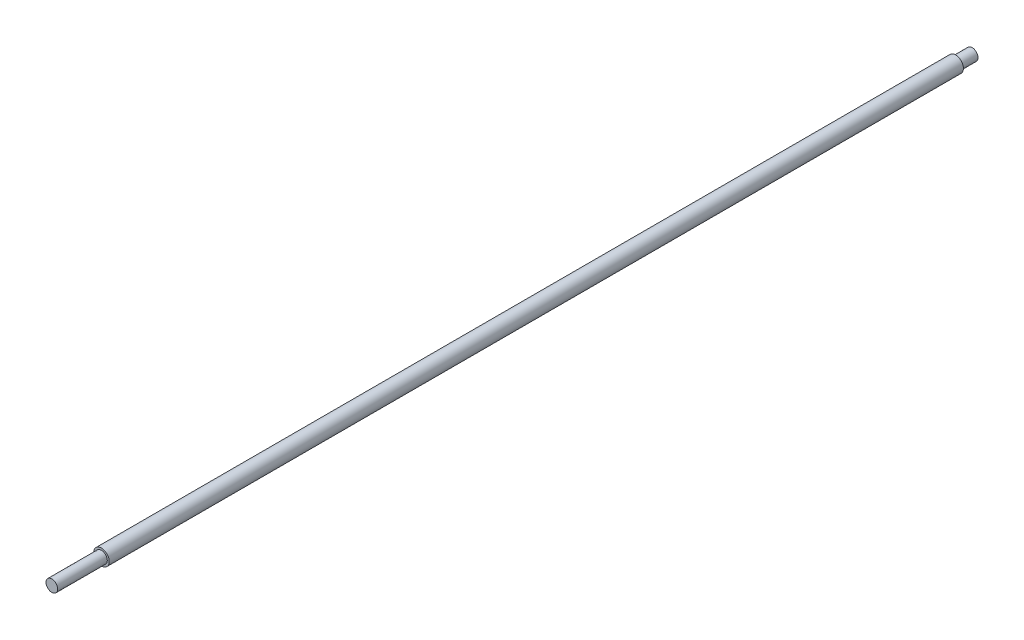
SolidWorks part; units mm, degrees
material "7079 Alloy"
ref_plane "Front" through (0, 0, 0) normal (0, 0, 1) x (1, 0, 0)
ref_plane "Top" through (0, 0, 0) normal (0, 1, 0) x (1, 0, 0)
ref_plane "Right" through (0, 0, 0) normal (1, 0, 0) x (0, 0, -1)
sketch "Sketch1" plane through (0, 0, 0) normal (0, 0, 1) x (1, 0, 0)
  circle A0 centre (0, 0) radius 8
extrude "Extrude1" add sketch "Sketch1" along normal blind 946
sketch "Sketch3" plane through (0, 0, 946) normal (0, 0, 1) x (1, 0, 0)
  circle A0 centre (0, 0) radius 6
  circle A1 centre (0, 0) radius 8
  circle M1 centre (0, 0) radius 8
extrude "Cut-Extrude1" cut sketch "Sketch3" against normal blind 54 contours A0 M1
sketch "Sketch4" plane through (0, 0, 0) normal (0, 0, -1) x (-1, 0, 0)
  circle A0 centre (0, 0) radius 6
  circle A1 centre (0, 0) radius 8
  circle M1 centre (0, 0) radius 8
extrude "Cut-Extrude2" cut sketch "Sketch4" against normal blind 20 contours A0 M1
sketch "Sketch5" plane through (0, 0, 20) normal (0, 0, -1) x (-1, 0, 0)
  circle A0 centre (0, 0) radius 8
  circle A1 centre (0, 0) radius 6
extrude "Extrude2" add sketch "Sketch5" along normal blind 3
sketch "Sketch6" plane through (0, 0, 892) normal (0, 0, 1) x (1, 0, 0)
  circle A0 centre (0, 0) radius 8
  circle A1 centre (0, 0) radius 6
extrude "Extrude3" add sketch "Sketch6" along normal blind 3
